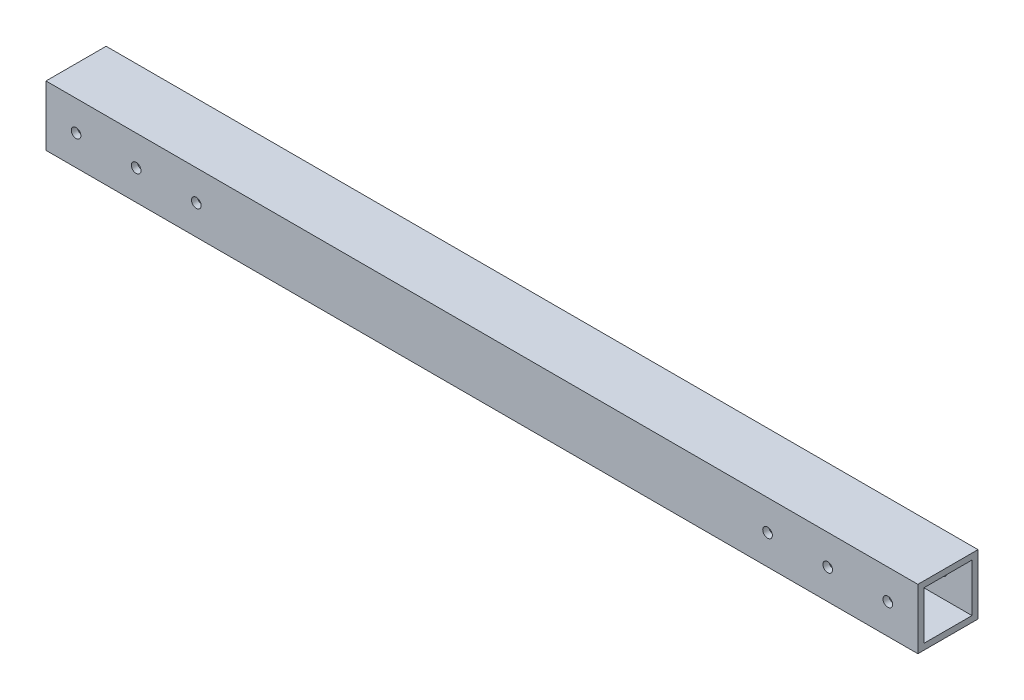
SolidWorks part; units mm, degrees
ref_plane "Front Plane" through (0, 0, 0) normal (0, 0, 1) x (1, 0, 0)
ref_plane "Top Plane" through (0, 0, 0) normal (0, 1, 0) x (1, 0, 0)
ref_plane "Right Plane" through (0, 0, 0) normal (1, 0, 0) x (0, 0, -1)
sketch "Sketch1" plane through (0, 0, 0) normal (0, 0, 1) x (1, 0, 0)
  line L0 (427.497, 210.002) -> (157.497, 210.002) construction
  line L1 (147.497, 210.002) -> (437.497, 210.002)
  line L2 (147.497, 210.002) -> (147.497, 190.002)
  line L3 (147.497, 190.002) -> (437.497, 190.002)
  line L4 (437.497, 210.002) -> (437.497, 190.002)
  line L5 (157.497, 190.002) -> (427.497, 190.002) construction
  line L6 (132.497, 165) -> (132.497, 145) construction
  line L7 (452.497, 145) -> (452.497, 165) construction
  dimension "D1" = 15
  dimension "D2" = 15
extrude "Extrude1" add sketch "Sketch1" along normal blind 20
sketch "Sketch2" plane through (147.497, 0, 0) normal (-1, 0, 0) x (0, 0, 1)
  line L0 (20, 210.002) -> (0, 210.002) construction
  line L1 (2, 208.002) -> (18, 208.002)
  line L2 (2, 208.002) -> (2, 192.002)
  line L3 (2, 192.002) -> (18, 192.002)
  line L4 (18, 208.002) -> (18, 192.002)
  line L5 (0, 210.002) -> (0, 190.002) construction
  dimension "D1" = 2
  dimension "D2" = 2
  dimension "D3" = 16
  dimension "D4" = 16
extrude "Cut-Extrude1" cut sketch "Sketch2" against normal blind 300
sketch "Sketch4" plane through (0, 0, 20) normal (0, 0, 1) x (1, 0, 0)
  circle A0 centre (427.497, 200.002) radius 1.6 construction
  circle A1 centre (407.497, 199.9525) radius 1.6 construction
  circle A2 centre (387.497, 199.9029) radius 1.6 construction
  circle A3 centre (197.497, 199.9029) radius 1.6 construction
  circle A4 centre (177.497, 199.9525) radius 1.6 construction
  circle A5 centre (157.497, 200.002) radius 1.6 construction
  circle A6 centre (427.497, 200.002) radius 1.6
  circle A7 centre (407.497, 199.9525) radius 1.6
  circle A8 centre (387.497, 199.9029) radius 1.6
  circle A9 centre (197.497, 199.9029) radius 1.6
  circle A10 centre (177.497, 199.9525) radius 1.6
  circle A11 centre (157.497, 200.002) radius 1.6
extrude "Cut-Extrude2" cut sketch "Sketch4" against normal blind 20
